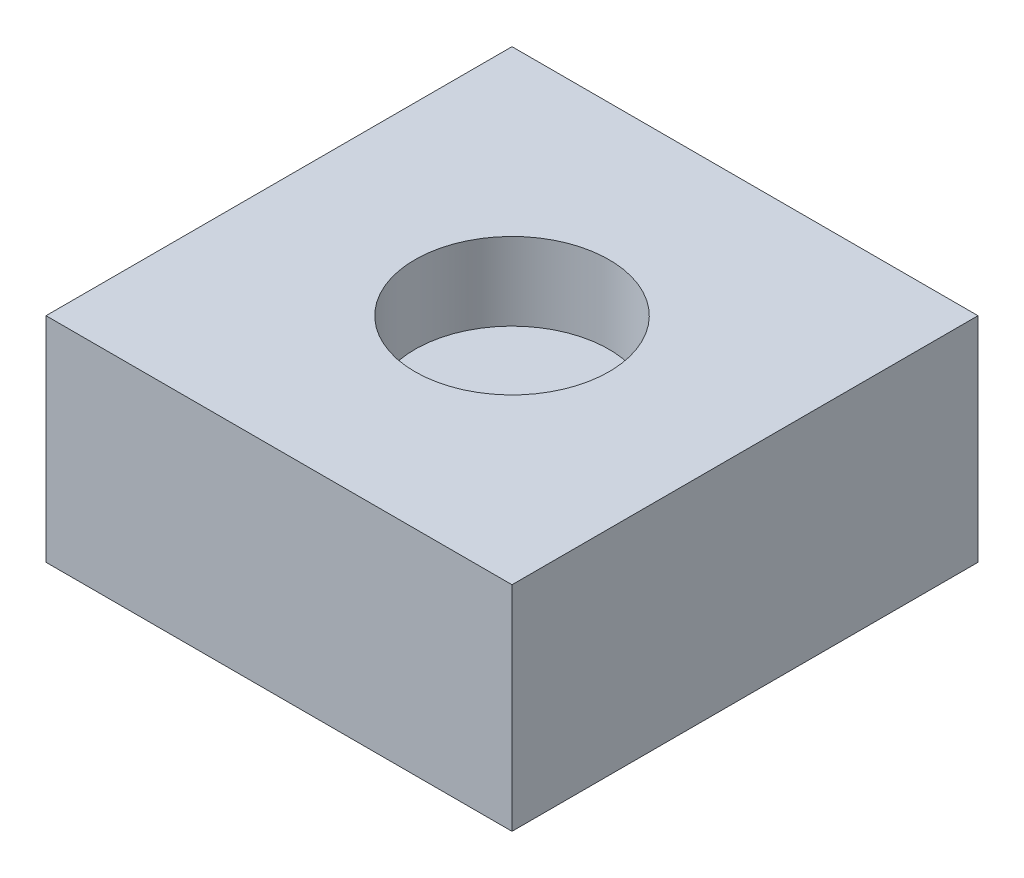
SolidWorks part; units mm, degrees
ref_plane "Front Plane" through (0, 0, 0) normal (0, 0, 1) x (1, 0, 0)
ref_plane "Top Plane" through (0, 0, 0) normal (0, 1, 0) x (1, 0, 0)
ref_plane "Right Plane" through (0, 0, 0) normal (1, 0, 0) x (0, 0, -1)
sketch "Sketch1" plane through (0, 0, 0) normal (0, 1, 0) x (1, 0, 0)
  line L1 (-6, -6) -> (6, -6)
  line L2 (-6, -6) -> (-6, 6)
  line L3 (-6, 6) -> (6, 6)
  line L4 (6, -6) -> (6, 6)
  line L5 (-6, -6) -> (6, 6) construction
  line L6 (-6, 6) -> (6, -6) construction
  point P0 (0, 0)
  dimension "D1" = 12
  dimension "D2" = 12
extrude "Boss-Extrude1" add sketch "Sketch1" along normal blind 5.5
sketch "Sketch2" plane through (0, 5.5, 0) normal (0, 1, 0) x (1, 0, 0)
  circle A0 centre (0, 0) radius 2.5
  dimension "D1" = 5
extrude "Cut-Extrude1" cut sketch "Sketch2" against normal blind 2
sketch "Sketch4" plane through (0, 0, 0) normal (0, -1, 0) x (1, 0, 0)
  circle A0 centre (0, 0) radius 1
  dimension "D1" = 2
extrude "Cut-Extrude3" cut sketch "Sketch4" against normal blind 2
fillet "Fillet2" radius 1 1 edges at (0, 2, -1)
